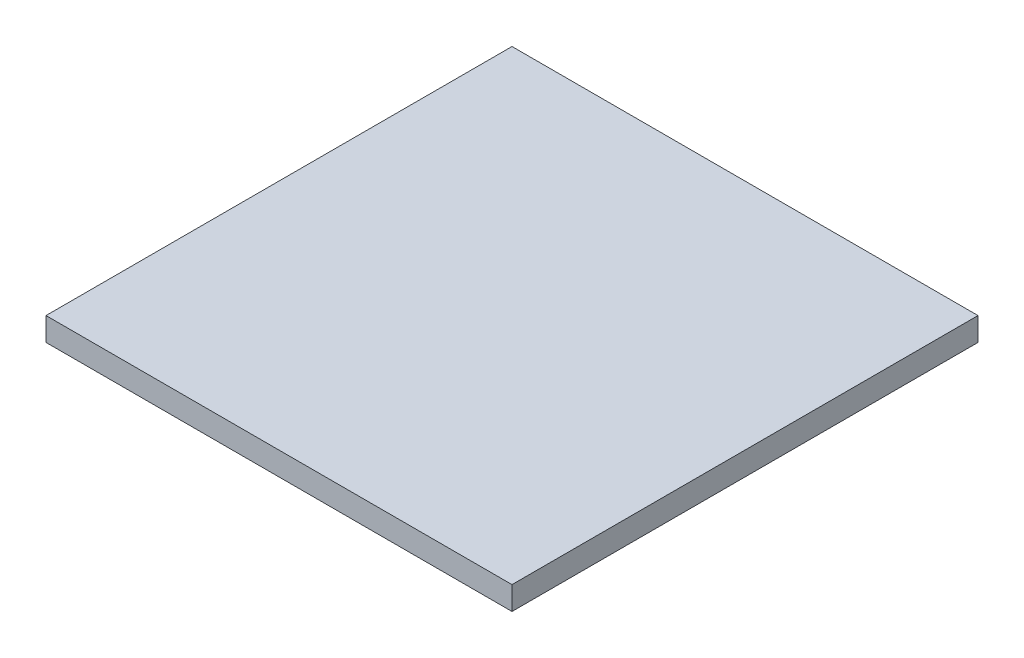
SolidWorks part; units mm, degrees
ref_plane "Front Plane" through (0, 0, 0) normal (0, 0, 1) x (1, 0, 0)
ref_plane "Top Plane" through (0, 0, 0) normal (0, 1, 0) x (1, 0, 0)
ref_plane "Right Plane" through (0, 0, 0) normal (1, 0, 0) x (0, 0, -1)
sketch "Sketch1" plane through (0, 0, 0) normal (0, 1, 0) x (1, 0, 0)
  line L1 (0, 0) -> (80, 0)
  line L2 (0, 0) -> (0, 80)
  line L3 (0, 80) -> (80, 80)
  line L4 (80, 0) -> (80, 80)
extrude "Boss-Extrude1" add sketch "Sketch1" along normal blind 4
